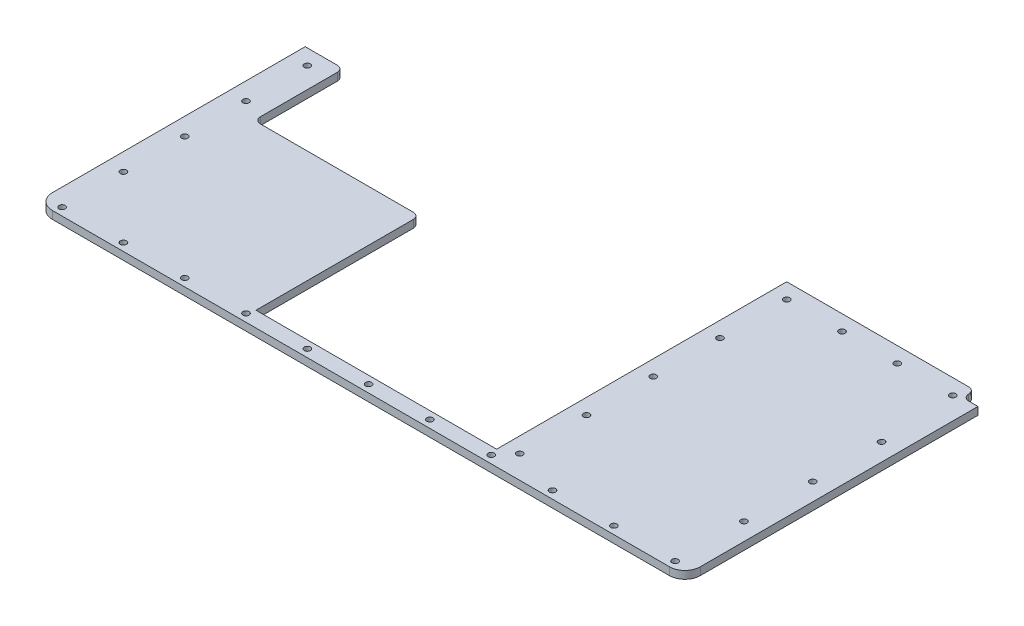
SolidWorks part; units mm, degrees
ref_plane "Front Plane" through (0, 0, 0) normal (0, 0, 1) x (1, 0, 0)
ref_plane "Top Plane" through (0, 0, 0) normal (0, 1, 0) x (1, 0, 0)
ref_plane "Right Plane" through (0, 0, 0) normal (1, 0, 0) x (0, 0, -1)
other "Bounding Box"
ref_plane "Default Plane" through (-8.9266, -12.7485, 0) normal (-0.1736, 0.9848, 0) x (0.9848, 0.1736, 0)
sketch "Sketch1" plane through (0, 0, 0) normal (0, 1, 0) x (1, 0, 0)
  line B0 (-66.675, 3.175) -> (-66.675, 55.2094)
  line B1 (-66.675, 55.2094) -> (-58.801, 55.2094)
  line B2 (-58.801, 55.2094) -> (-58.801, 36.83)
  line B3 (-58.801, 36.83) -> (-24.765, 36.83)
  line B4 (-24.765, 36.83) -> (-24.765, 3.175)
  line B5 (-24.765, 3.175) -> (24.765, 3.175)
  line B6 (24.765, 3.175) -> (24.765, 62.865)
  line B7 (24.765, 62.865) -> (62.23, 62.865)
  line B8 (-63.5, 0) -> (63.5, 0)
  line B9 (64.77, 60.325) -> (66.675, 60.325)
  line B10 (66.675, 60.325) -> (66.675, 3.175)
  arc B11 (66.675, 3.175) -> (63.5, 0) centre (63.5, 3.175) cw
  arc B12 (-63.5, 0) -> (-66.675, 3.175) centre (-63.5, 3.175) cw
  arc B13 (62.23, 62.865) -> (63.5, 61.595) centre (62.23, 61.595) cw
  arc B14 (63.5, 61.595) -> (64.77, 60.325) centre (64.77, 61.595) ccw
sketch_block_instance "Center Top plate-1"
sketch_block "Center Top plate" parameters "D3"=3.175, "D4"=3.175, "D1"=36.83, "D2"=7.874
extrude "Boss-Extrude1" add sketch "Sketch1" along normal blind 1.5875
fillet "Fillet1" radius 1.27 3 edges at (-24.765, 0.7937, -36.83) (-58.801, 0.7937, -36.83) (-58.801, 0.7937, -55.2094)
sketch "Sketch2" plane through (0, 1.5875, 0) normal (0, 1, 0) x (-1, 0, 0)
  line L0 (66.2496, -1.5875) -> (-66.2496, -1.5875) construction
  line L2 (63.5, 0) -> (-63.5, 0) construction
  line L3 (63.0746, -1.5875) -> (63.0746, -55.2094) construction
  line L4 (60.071, -55.2094) -> (66.675, -55.2094) construction
  line L5 (-63.0746, -1.5875) -> (-63.0746, -58.8729) construction
  line L6 (-63.0746, -58.8729) -> (-62.1009, -59.69) construction
  line L7 (-62.1009, -59.69) -> (-27.94, -59.69) construction
  line L8 (-27.94, -59.69) -> (-27.94, -4.7625) construction
  line L10 (-62.23, -62.865) -> (-24.765, -62.865) construction
  line L11 (-24.765, -62.865) -> (-24.765, -3.175) construction
  arc A0 (66.675, -3.175) -> (63.5, 0) centre (63.5, -3.175) ccw construction
  arc A1 (-63.5, 0) -> (-66.675, -3.175) centre (-63.5, -3.175) ccw construction
  circle A2 centre (63.0746, -1.5875) radius 0.635
  circle A3 centre (50.4597, -1.5875) radius 0.635
  circle A4 centre (37.8448, -1.5875) radius 0.635
  circle A5 centre (25.2299, -1.5875) radius 0.635
  circle A6 centre (12.6149, -1.5875) radius 0.635
  circle A7 centre (0, -1.5875) radius 0.635
  circle A8 centre (-12.6149, -1.5875) radius 0.635
  circle A9 centre (-25.2299, -1.5875) radius 0.635
  circle A10 centre (-37.8448, -1.5875) radius 0.635
  circle A11 centre (-50.4597, -1.5875) radius 0.635
  circle A12 centre (-63.0746, -1.5875) radius 0.635
  circle A13 centre (63.0746, -14.1992) radius 0.635
  circle A14 centre (63.0746, -26.8109) radius 0.635
  circle A15 centre (63.0746, -39.4226) radius 0.635
  circle A16 centre (63.0746, -52.0344) radius 0.635
  arc A17 (-63.5, -61.595) -> (-64.77, -60.325) centre (-64.77, -61.595) ccw construction
  circle A18 centre (-63.0746, -15.7501) radius 0.635
  circle A19 centre (-63.0746, -29.9127) radius 0.635
  circle A20 centre (-63.0746, -44.0753) radius 0.635
  circle A22 centre (-62.1009, -59.69) radius 0.635
  circle A23 centre (-50.7139, -59.69) radius 0.635
  circle A24 centre (-39.327, -59.69) radius 0.635
  circle A25 centre (-27.94, -59.69) radius 0.635
  circle A26 centre (-27.94, -45.9581) radius 0.635
  circle A27 centre (-27.94, -32.2263) radius 0.635
  circle A28 centre (-27.94, -18.4944) radius 0.635
  circle A29 centre (-27.94, -4.7625) radius 0.635
  point P62 (-27.94, -45.9581)
  point P63 (-62.1009, -59.69)
  dimension "D2" = 1.27
  dimension "D1" = 1.5875
  dimension "D3" = 3.175
  dimension "D5" = 3.175
  dimension "D6" = 5
  dimension "D7" = 3.175
  dimension "D8" = 3.175
  dimension "D9" = 3.175
  dimension "D10" = 3.175
  dimension "D11" = 130
  dimension "D16" = 3.175
  dimension "D17" = 14.1626
  dimension "D18" = 14.1626
  dimension "D19" = 14.1626
  dimension "D4" = 11
  dimension "D14" = 4
  dimension "D15" = 5
extrude "Cut-Extrude1" cut sketch "Sketch2" against normal through all both and the other way through all
